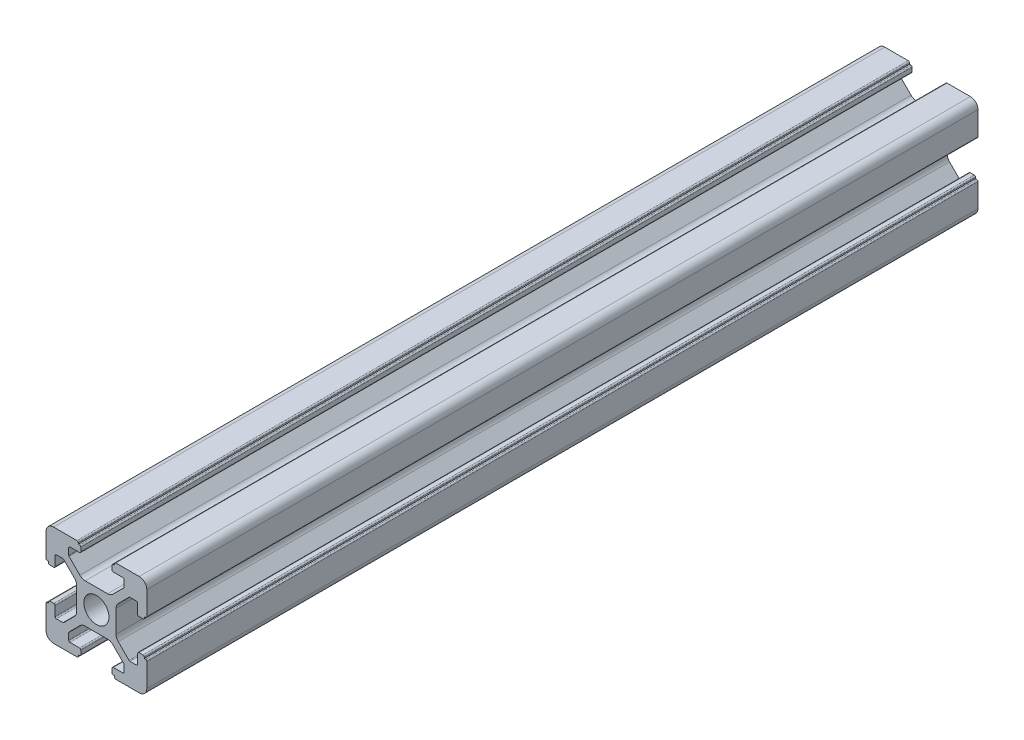
SolidWorks part; units mm, degrees
ref_plane "前视基准面" through (0, 0, 0) normal (0, 0, 1) x (1, 0, 0)
ref_plane "上视基准面" through (0, 0, 0) normal (0, 1, 0) x (1, 0, 0)
ref_plane "右视基准面" through (0, 0, 0) normal (1, 0, 0) x (0, 0, -1)
sketch "草图1" plane through (0, 0, 0) normal (0, 0, 1) x (1, 0, 0)
  line L0 (0, 0) -> (0, 5.5) construction
  line L1 (-8.5023, -10.0023) -> (-3.85, -10.0023)
  line L2 (-10.0023, -8.5023) -> (-10.0023, -3.85)
  line L3 (-8.5023, 10.0023) -> (-3.85, 10.0023)
  line L4 (10.0023, -8.5023) -> (10.0023, -3.85)
  line L5 (-10.0023, -10.0023) -> (10.0023, 10.0023) construction
  line L6 (-10.0023, 10.0023) -> (10.0023, -10.0023) construction
  line L7 (-2.218, -3.9) -> (2.218, -3.9)
  line L8 (-3.9, -2.218) -> (-3.9, 2.218)
  line L9 (-2.218, 3.9) -> (2.218, 3.9)
  line L10 (3.9, -2.218) -> (3.9, 2.218)
  line L11 (-3.9, -3.9) -> (3.9, 3.9) construction
  line L12 (-3.9, 3.9) -> (3.9, -3.9) construction
  line L13 (-5.25, -8.2) -> (-3.35, -8.2)
  line L14 (-8.2, -5.25) -> (-8.2, -3.35)
  line L15 (-5.25, 8.2) -> (-3.35, 8.2)
  line L16 (8.2, -5.25) -> (8.2, -3.35)
  line L17 (-8.2, -8.2) -> (8.2, 8.2) construction
  line L18 (-8.2, 8.2) -> (8.2, -8.2) construction
  line L19 (-7.95, 5.5) -> (-6.6642, 5.5)
  line L20 (0, 0) -> (5.5, 0) construction
  line L23 (-5.5, 7.95) -> (-5.5, 6.6642)
  line L26 (0, 0) -> (-0.5303, 0.5303)
  line L27 (3.2787, 4.3393) -> (5.4268, 6.4874)
  line L28 (0, 0) -> (0.5303, -0.5303)
  line L29 (5.5, 6.6642) -> (5.5, 7.95)
  line L30 (4.3393, 3.2787) -> (6.4874, 5.4268)
  line L31 (6.6642, 5.5) -> (7.95, 5.5)
  line L32 (4.3393, -3.2787) -> (6.4874, -5.4268)
  line L33 (3.2787, -4.3393) -> (5.4268, -6.4874)
  line L34 (-3.2787, -4.3393) -> (-5.4268, -6.4874)
  line L35 (-4.3393, -3.2787) -> (-6.4874, -5.4268)
  line L36 (-4.3393, 3.2787) -> (-6.4874, 5.4268)
  line L37 (-3.2787, 4.3393) -> (-5.4268, 6.4874)
  line L38 (3.1, -8.45) -> (3.1, -9.2523)
  line L39 (8.45, 3.1) -> (9.2523, 3.1)
  line L40 (-5.5, -6.6642) -> (-5.5, -7.95)
  line L41 (-6.6642, -5.5) -> (-7.95, -5.5)
  line L42 (5.5, -6.6642) -> (5.5, -7.95)
  line L43 (6.6642, -5.5) -> (7.95, -5.5)
  line L44 (9.2523, -3.1) -> (8.45, -3.1)
  line L46 (10.0023, 3.85) -> (10.0023, 8.5023)
  line L47 (8.2, 3.35) -> (8.2, 5.25)
  line L48 (-3.1, -9.2523) -> (-3.1, -8.45)
  line L49 (-8.45, -3.1) -> (-9.2523, -3.1)
  line L50 (-9.2523, 3.1) -> (-8.45, 3.1)
  line L51 (-3.1, 8.45) -> (-3.1, 9.2523)
  line L52 (3.1, 9.2523) -> (3.1, 8.45)
  line L53 (3.85, 10.0023) -> (8.5023, 10.0023)
  line L54 (3.35, 8.2) -> (5.25, 8.2)
  line L55 (-10.0023, 3.85) -> (-10.0023, 8.5023)
  line L56 (-8.2, 3.35) -> (-8.2, 5.25)
  line L57 (3.35, -8.2) -> (5.25, -8.2)
  line L58 (3.85, -10.0023) -> (8.5023, -10.0023)
  line L59 (9.7523, -3.6) -> (9.5023, -3.6)
  line L61 (9.7523, 3.6) -> (9.5023, 3.6)
  line L62 (9.5023, -3.6) -> (9.5023, -3.35)
  line L63 (3.6, -9.7523) -> (3.6, -9.5023)
  line L64 (3.35, -9.5023) -> (3.6, -9.5023)
  line L65 (9.5023, 3.35) -> (9.5023, 3.6)
  line L66 (-3.6, -9.5023) -> (-3.35, -9.5023)
  line L67 (-3.6, -9.7523) -> (-3.6, -9.5023)
  line L68 (-9.7523, -3.6) -> (-9.5023, -3.6)
  line L69 (-9.5023, -3.35) -> (-9.5023, -3.6)
  line L70 (-9.5023, 3.6) -> (-9.5023, 3.35)
  line L71 (-9.7523, 3.6) -> (-9.5023, 3.6)
  line L72 (-3.6, 9.7523) -> (-3.6, 9.5023)
  line L73 (-3.35, 9.5023) -> (-3.6, 9.5023)
  line L74 (3.6, 9.5023) -> (3.35, 9.5023)
  line L75 (3.6, 9.7523) -> (3.6, 9.5023)
  circle A0 centre (0, 0) radius 2.5
  arc A1 (10.0023, 8.5023) -> (8.5023, 10.0023) centre (8.5023, 8.5023) ccw
  arc A2 (8.5023, -10.0023) -> (10.0023, -8.5023) centre (8.5023, -8.5023) ccw
  arc A3 (-10.0023, -8.5023) -> (-8.5023, -10.0023) centre (-8.5023, -8.5023) ccw
  arc A4 (-10.0023, 8.5023) -> (-8.5023, 10.0023) centre (-8.5023, 8.5023) cw
  arc A5 (-9.5023, -3.35) -> (-9.2523, -3.1) centre (-9.2523, -3.35) cw
  arc A6 (-9.7523, -3.6) -> (-10.0023, -3.85) centre (-9.7523, -3.85) ccw
  arc A7 (-8.45, -3.1) -> (-8.2, -3.35) centre (-8.45, -3.35) cw
  arc A8 (-7.95, -5.5) -> (-8.2, -5.25) centre (-7.95, -5.25) cw
  arc A9 (-6.4874, -5.4268) -> (-6.6642, -5.5) centre (-6.6642, -5.25) cw
  arc A10 (-5.4268, -6.4874) -> (-5.5, -6.6642) centre (-5.25, -6.6642) ccw
  arc A11 (-5.5, -7.95) -> (-5.25, -8.2) centre (-5.25, -7.95) ccw
  arc A12 (-3.6, -9.7523) -> (-3.85, -10.0023) centre (-3.85, -9.7523) cw
  arc A13 (-3.35, -9.5023) -> (-3.1, -9.2523) centre (-3.35, -9.2523) ccw
  arc A14 (-3.1, -8.45) -> (-3.35, -8.2) centre (-3.35, -8.45) ccw
  arc A15 (3.1, -8.45) -> (3.35, -8.2) centre (3.35, -8.45) cw
  arc A16 (5.5, -7.95) -> (5.25, -8.2) centre (5.25, -7.95) cw
  arc A17 (5.4268, -6.4874) -> (5.5, -6.6642) centre (5.25, -6.6642) cw
  arc A18 (6.4874, -5.4268) -> (6.6642, -5.5) centre (6.6642, -5.25) ccw
  arc A19 (7.95, -5.5) -> (8.2, -5.25) centre (7.95, -5.25) ccw
  arc A20 (8.45, -3.1) -> (8.2, -3.35) centre (8.45, -3.35) ccw
  arc A21 (9.5023, -3.35) -> (9.2523, -3.1) centre (9.2523, -3.35) ccw
  arc A22 (9.7523, -3.6) -> (10.0023, -3.85) centre (9.7523, -3.85) cw
  arc A23 (3.35, -9.5023) -> (3.1, -9.2523) centre (3.35, -9.2523) cw
  arc A24 (3.6, -9.7523) -> (3.85, -10.0023) centre (3.85, -9.7523) ccw
  arc A25 (7.95, 5.5) -> (8.2, 5.25) centre (7.95, 5.25) cw
  arc A26 (8.2, 3.35) -> (8.45, 3.1) centre (8.45, 3.35) ccw
  arc A27 (9.5023, 3.35) -> (9.2523, 3.1) centre (9.2523, 3.35) cw
  arc A28 (9.7523, 3.6) -> (10.0023, 3.85) centre (9.7523, 3.85) ccw
  arc A29 (6.6642, 5.5) -> (6.4874, 5.4268) centre (6.6642, 5.25) ccw
  arc A30 (5.4268, 6.4874) -> (5.5, 6.6642) centre (5.25, 6.6642) ccw
  arc A31 (5.5, 7.95) -> (5.25, 8.2) centre (5.25, 7.95) ccw
  arc A32 (3.1, 8.45) -> (3.35, 8.2) centre (3.35, 8.45) ccw
  arc A33 (3.6, 9.7523) -> (3.85, 10.0023) centre (3.85, 9.7523) cw
  arc A34 (3.35, 9.5023) -> (3.1, 9.2523) centre (3.35, 9.2523) ccw
  arc A35 (-9.7523, 3.6) -> (-10.0023, 3.85) centre (-9.7523, 3.85) cw
  arc A36 (-9.5023, 3.35) -> (-9.2523, 3.1) centre (-9.2523, 3.35) ccw
  arc A37 (-8.45, 3.1) -> (-8.2, 3.35) centre (-8.45, 3.35) ccw
  arc A38 (-8.2, 5.25) -> (-7.95, 5.5) centre (-7.95, 5.25) cw
  arc A39 (-6.4874, 5.4268) -> (-6.6642, 5.5) centre (-6.6642, 5.25) ccw
  arc A40 (-5.4268, 6.4874) -> (-5.5, 6.6642) centre (-5.25, 6.6642) cw
  arc A41 (-5.5, 7.95) -> (-5.25, 8.2) centre (-5.25, 7.95) cw
  arc A42 (-3.1, 8.45) -> (-3.35, 8.2) centre (-3.35, 8.45) cw
  arc A43 (-3.1, 9.2523) -> (-3.35, 9.5023) centre (-3.35, 9.2523) ccw
  arc A44 (-3.6, 9.7523) -> (-3.85, 10.0023) centre (-3.85, 9.7523) ccw
  arc A45 (-4.3393, 3.2787) -> (-3.9, 2.218) centre (-5.4, 2.218) cw
  arc A46 (-3.2787, 4.3393) -> (-2.218, 3.9) centre (-2.218, 5.4) ccw
  arc A47 (3.2787, 4.3393) -> (2.218, 3.9) centre (2.218, 5.4) cw
  arc A48 (4.3393, 3.2787) -> (3.9, 2.218) centre (5.4, 2.218) ccw
  arc A49 (4.3393, -3.2787) -> (3.9, -2.218) centre (5.4, -2.218) cw
  arc A50 (3.2787, -4.3393) -> (2.218, -3.9) centre (2.218, -5.4) ccw
  arc A51 (-4.3393, -3.2787) -> (-3.9, -2.218) centre (-5.4, -2.218) ccw
  arc A52 (-2.218, -3.9) -> (-3.2787, -4.3393) centre (-2.218, -5.4) ccw
  point P0 (0, 0)
  point P7 (10.0023, 0)
  point P62 (0, 0)
  point P76 (0, 0)
  point P92 (-8.2, -5.5)
  point P99 (0, 0)
  point P106 (-5.5, -8.2)
  point P117 (5.5, -8.2)
  point P124 (8.2, -5.5)
  point P137 (8.2, 5.5)
  point P140 (8.2, 3.1)
  point P147 (6.5607, 5.5)
  point P152 (5.5, 8.2)
  point P167 (-8.2, 5.5)
  point P174 (-5.5, 8.2)
  dimension "D1" = 1.5
  dimension "D5" = 0.25
  dimension "D6" = 1.5
  dimension "D2" = 4
  dimension "D3" = 4
  dimension "D4" = 4
extrude "凸台-拉伸1" add sketch "草图1" along normal blind 165 contours A52 L7 A50 L33 A17 L42 A16 L57 A15 L38 A23 L64 L63 A24 L58 A2 L4 A22 L59 L62 A21 L44 A20 L16 A19 L43 A18 L32 A49 L10 A48 L30 A29 L31 A25 L47 A26 L39 A27 L65 L61 A28 L46 A1 L53 A33 L75 L74 A34 L52 A32
